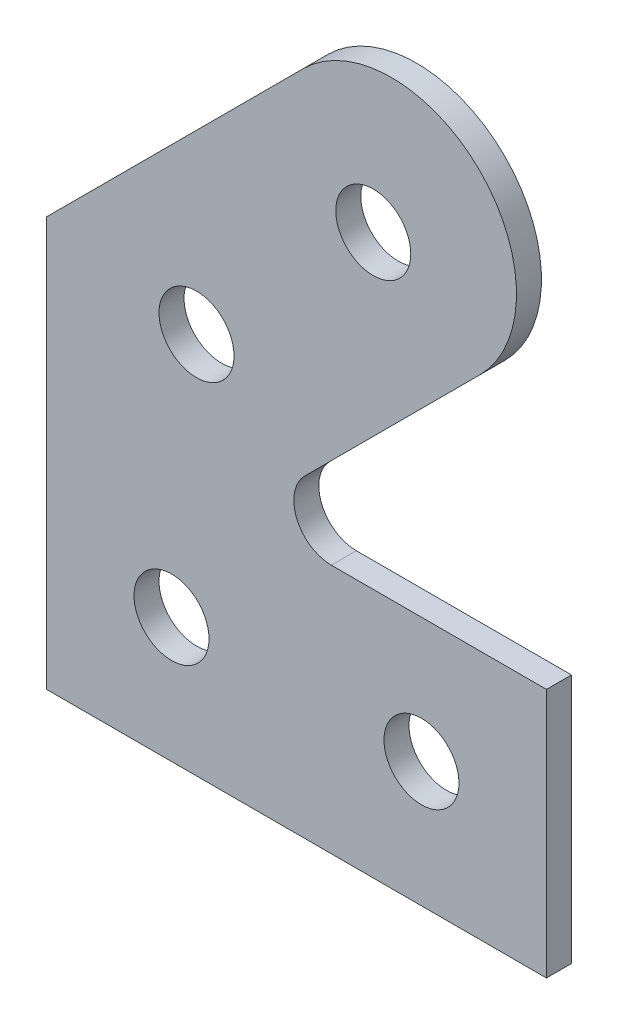
SolidWorks part; units mm, degrees
ref_plane "Front Plane" through (0, 0, 0) normal (0, 0, 1) x (1, 0, 0)
ref_plane "Top Plane" through (0, 0, 0) normal (0, 1, 0) x (1, 0, 0)
ref_plane "Right Plane" through (0, 0, 0) normal (1, 0, 0) x (0, 0, -1)
sketch "Esquisse1" plane through (0, 0, 0) normal (0, 0, 1) x (1, 0, 0)
  line L0 (0, 0) -> (20, 0)
  line L1 (20, 0) -> (20, 10)
  line L2 (20, 10) -> (11.3924, 10)
  line L3 (0, 0) -> (0, 16.3711)
  line L4 (0, 16.3711) -> (10.2645, 26.6355)
  line L5 (10.3317, 12.5607) -> (17.3355, 19.5645)
  arc A0 (10.2645, 26.6355) -> (17.3355, 19.5645) centre (13.8, 23.1) cw
  arc A1 (11.3924, 10) -> (10.3317, 12.5607) centre (11.3924, 11.5) cw
  circle A2 centre (5, 5) radius 1.5
  circle A3 centre (15, 5) radius 1.5
  circle A4 centre (6, 15.3) radius 1.5
  circle A5 centre (13.0711, 22.3711) radius 1.5
  point P13 (20, 5)
  point P20 (0, 0)
  point P21 (6.9784, 16.3711)
  point P22 (0, 0)
  point P23 (0, 0)
  point P24 (7.0743, 16.3711)
  dimension "D7" = 1.5
  dimension "D8" = 3
  dimension "D1" = 10
  dimension "D2" = 20
  dimension "D3" = 135
  dimension "D4" = 10
  dimension "D5" = 13.8
  dimension "D6" = 23.1
  dimension "D9" = 5
  dimension "D10" = 10
  dimension "D11" = 5
  dimension "D12" = 5
  dimension "D13" = 10
  dimension "D14" = 1
extrude "Boss.-Extru.1" add sketch "Esquisse1" along normal blind 1
